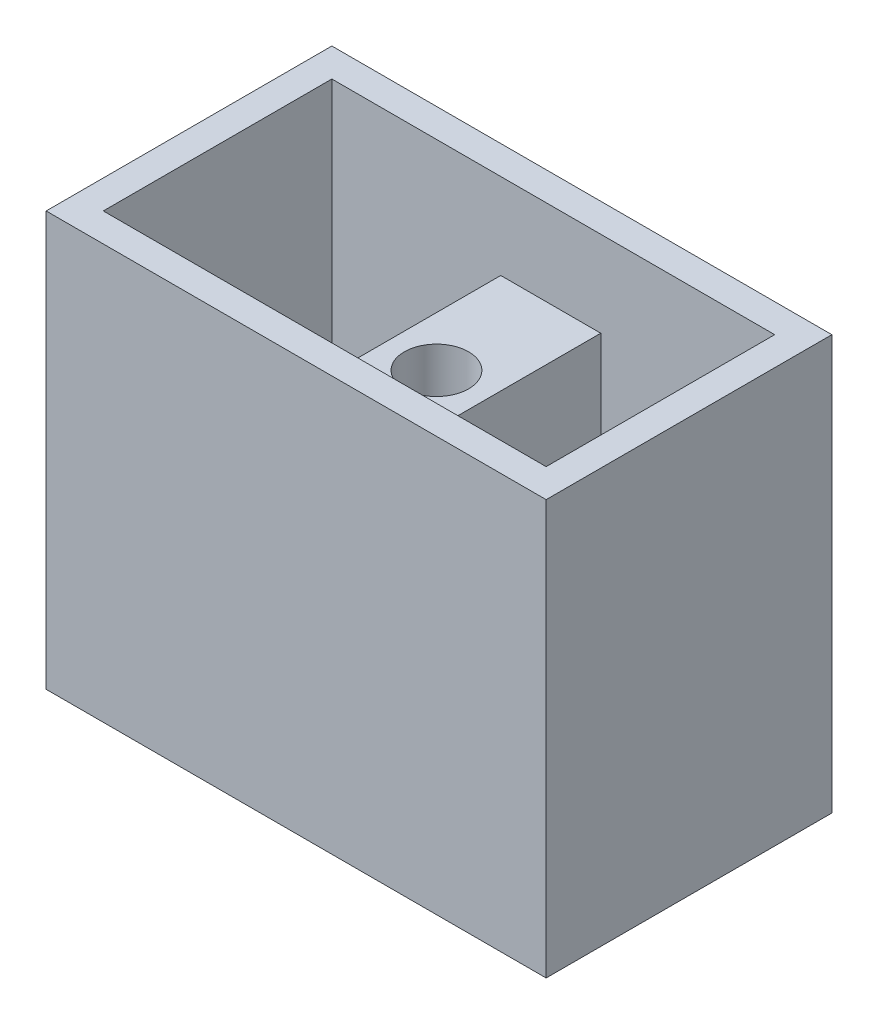
SolidWorks part; units mm, degrees
ref_plane "Front Plane" through (0, 0, 0) normal (0, 0, 1) x (1, 0, 0)
ref_plane "Top Plane" through (0, 0, 0) normal (0, 1, 0) x (1, 0, 0)
ref_plane "Right Plane" through (0, 0, 0) normal (1, 0, 0) x (0, 0, -1)
sketch "Sketch1" plane through (0, 0, 0) normal (0, 1, 0) x (1, 0, 0)
  line L1 (0, 0) -> (175, 0)
  line L2 (0, 0) -> (0, 100)
  line L3 (0, 100) -> (175, 100)
  line L4 (175, 0) -> (175, 100)
  dimension "D1" = 175
  dimension "D2" = 100
extrude "Boss-Extrude1" add sketch "Sketch1" along normal blind 145
sketch "Sketch2" plane through (0, 145, 0) normal (0, 1, 0) x (1, 0, 0)
  line L10 (69.1133, 90) -> (69.1133, 10)
  line L11 (104.1133, 90) -> (104.1133, 10)
  line L12 (86.6133, 86.4407) -> (86.6133, -12.5064) construction
  line L13 (69.1133, 90) -> (10, 90)
  line L14 (10, 10) -> (165, 10)
  line L15 (165, 10) -> (165, 90)
  line L16 (165, 90) -> (10, 90)
  line L17 (10, 90) -> (10, 10)
  line L18 (10, 10) -> (69.1133, 10)
  line L19 (165, 10) -> (165, 90)
  line L20 (165, 90) -> (104.1133, 90)
  line L21 (10, 90) -> (10, 10)
  line L22 (104.1133, 10) -> (165, 10)
  circle A0 centre (86.6133, 50) radius 11.25
  point P12 (0, 0)
  point P13 (104.1133, 50)
  dimension "D3" = 22.5
  dimension "D2" = 35
  dimension "D1" = 10
extrude "Cut-Extrude1" cut sketch "Sketch2" against normal blind 145
sketch "Sketch4" plane through (0, 145, 0) normal (0, 1, 0) x (1, 0, 0)
  line L3 (69.1133, 90) -> (104.1133, 90)
  line L4 (69.1133, 90) -> (69.1133, 10)
  line L5 (69.1133, 10) -> (104.1133, 10)
  line L6 (104.1133, 90) -> (104.1133, 10)
extrude "Cut-Extrude2" cut sketch "Sketch4" against normal blind 30
sketch "Sketch5" plane through (0, 0, 0) normal (0, -1, 0) x (1, 0, 0)
  line L1 (69.1133, -10) -> (104.1133, -10)
  line L2 (69.1133, -10) -> (69.1133, -90)
  line L3 (69.1133, -90) -> (104.1133, -90)
  line L4 (104.1133, -10) -> (104.1133, -90)
extrude "Cut-Extrude3" cut sketch "Sketch5" against normal blind 30
